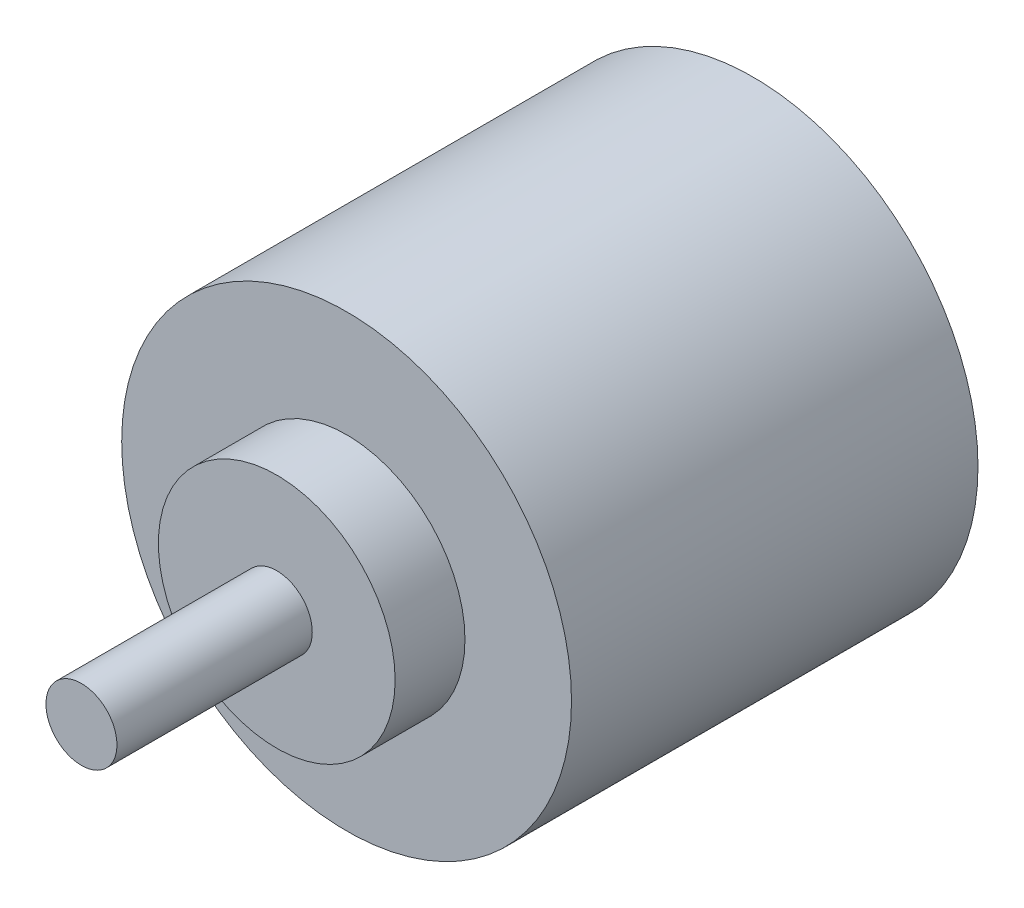
SolidWorks part; units mm, degrees
ref_plane "前视基准面" through (0, 0, 0) normal (0, 0, 1) x (1, 0, 0)
ref_plane "上视基准面" through (0, 0, 0) normal (0, 1, 0) x (1, 0, 0)
ref_plane "右视基准面" through (0, 0, 0) normal (1, 0, 0) x (0, 0, -1)
other "Configuration Table"
sketch "Sketch1" plane through (0, 0, 0) normal (0, 0, 1) x (1, 0, 0)
  circle A0 centre (0, 0) radius 19
  dimension "D1" = 38
extrude "Boss-Extrude1" add sketch "Sketch1" along normal blind 34.34
sketch "Sketch2" plane through (0, 0, 34.34) normal (0, 0, 1) x (1, 0, 0)
  circle A0 centre (0, 0) radius 10
  dimension "D1" = 20
extrude "Boss-Extrude2" add sketch "Sketch2" along normal blind 5.9
sketch "Sketch3" plane through (0, 0, 40.24) normal (0, 0, 1) x (1, 0, 0)
  circle A0 centre (0, 0) radius 3
  dimension "D1" = 6
extrude "Boss-Extrude3" add sketch "Sketch3" along normal blind 16.5
